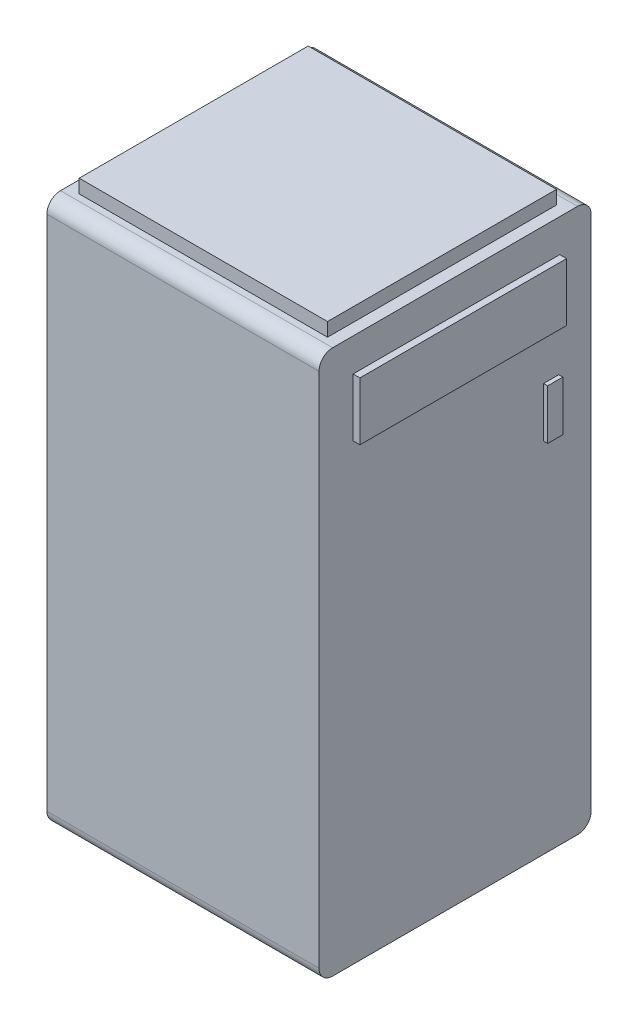
SolidWorks part; units mm, degrees
ref_plane "Front Plane" through (0, 0, 0) normal (0, 0, 1) x (1, 0, 0)
ref_plane "Top Plane" through (0, 0, 0) normal (0, 1, 0) x (1, 0, 0)
ref_plane "Right Plane" through (0, 0, 0) normal (1, 0, 0) x (0, 0, -1)
sketch "Sketch1" plane through (0, 0, 0) normal (0, 1, 0) x (1, 0, 0)
  line L1 (0, 0) -> (-200, 0)
  line L2 (0, 0) -> (0, 200)
  line L3 (0, 200) -> (-200, 200)
  line L4 (-200, 0) -> (-200, 200)
  dimension "D1" = 200
  dimension "D2" = 200
extrude "Boss-Extrude1" add sketch "Sketch1" along normal blind 400
fillet "Fillet1" radius 10 1 edges at (-100, 400, 0)
fillet "Fillet2" radius 10 1 edges at (-100, 400, -200)
fillet "Fillet3" radius 10 1 edges at (-100, 0, 0)
fillet "Fillet4" radius 10 1 edges at (-100, 0, -200)
sketch "Sketch2" plane through (0, 0, 0) normal (1, 0, 0) x (0, 0, -1)
  line L1 (25.0722, 375.7821) -> (176.963, 375.7821)
  line L2 (25.0722, 375.7821) -> (25.0722, 333.1762)
  line L3 (25.0722, 333.1762) -> (176.963, 333.1762)
  line L4 (176.963, 375.7821) -> (176.963, 333.1762)
  point P4 (163.1801, 375.2476)
  point P5 (25.0722, 375.7821)
  point P6 (176.963, 375.7821)
extrude "Boss-Extrude2" add sketch "Sketch2" along normal blind 5
sketch "Sketch3" plane through (0, 0, 0) normal (1, 0, 0) x (0, 0, -1)
  line L0 (165.0704, 299.7166) -> (176.2482, 299.7166)
  line L1 (176.2482, 299.7166) -> (176.2482, 263.0207)
  line L2 (176.2482, 263.0207) -> (165.0704, 263.0207)
  line L3 (165.0704, 263.0207) -> (165.0704, 299.7166)
  point P2 (164.8503, 278.3754)
extrude "Boss-Extrude3" add sketch "Sketch3" along normal blind 3
sketch "Sketch4" plane through (0, 400, 0) normal (0, 1, 0) x (1, 0, 0)
  line L0 (-191.056, 183.0833) -> (-8.5608, 183.0833)
  line L1 (-8.5608, 183.0833) -> (-8.5608, 14.8092)
  line L2 (-8.5608, 14.8092) -> (-191.056, 14.8092)
  line L3 (-191.056, 14.8092) -> (-191.056, 183.0833)
  point P2 (-191.056, 183.0833)
extrude "Cut-Extrude1" cut sketch "Sketch4" against normal blind 350
sketch "Sketch5" plane through (0, 50, 0) normal (0, 1, 0) x (1, 0, 0)
  line L0 (-191.056, 183.0833) -> (-8.5608, 183.0833)
  line L1 (-8.5608, 183.0833) -> (-8.5608, 14.8092)
  line L2 (-8.5608, 14.8092) -> (-191.056, 14.8092)
  line L3 (-191.056, 14.8092) -> (-191.056, 183.0833)
extrude "Cut-Extrude2" cut sketch "Sketch5" against normal blind 175
ref_plane "Plane1" through (0, 400, 0) normal (0, 1, 0) x (1, 0, 0)
sketch "Sketch6" plane through (0, 400, 0) normal (0, 1, 0) x (1, 0, 0)
  line L0 (-191.056, 183.0833) -> (-8.5608, 183.0833)
  line L1 (-8.5608, 183.0833) -> (-8.5608, 14.8092)
  line L2 (-8.5608, 14.8092) -> (-191.056, 14.8092)
  line L3 (-191.056, 14.8092) -> (-191.056, 183.0833)
extrude "Boss-Extrude4" add sketch "Sketch6" along normal blind 10 separate body
